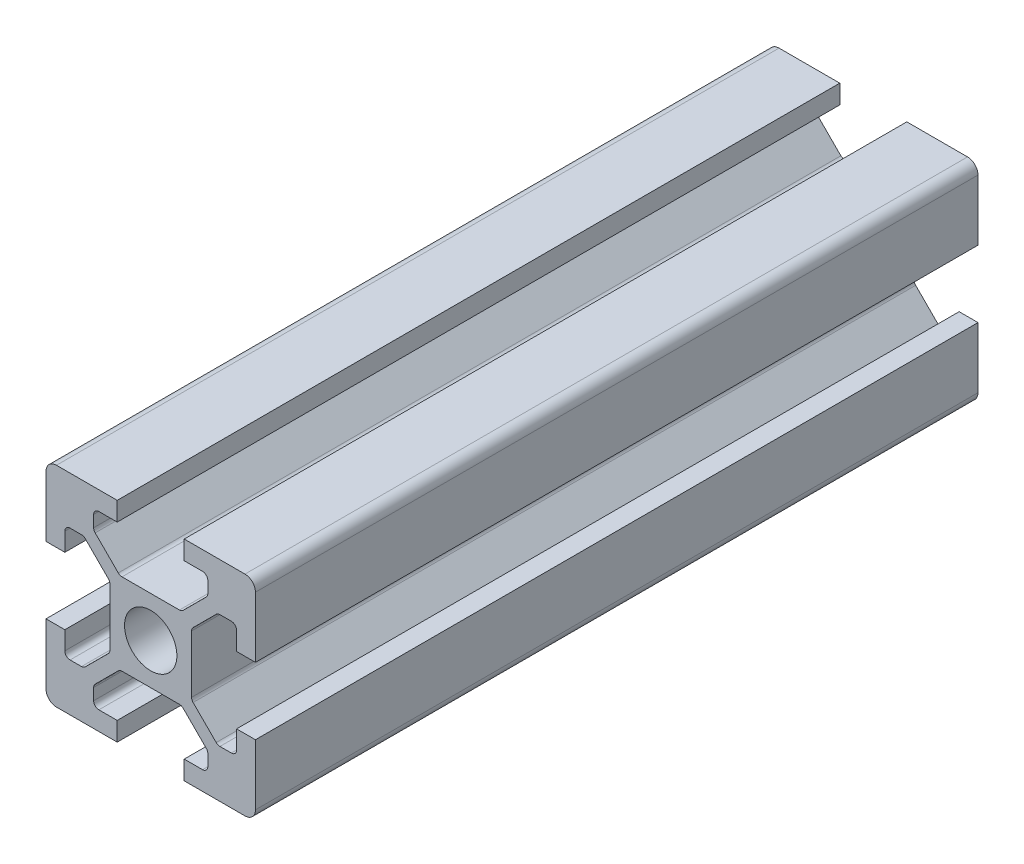
SolidWorks part; units mm, degrees
material "1060 Alloy"
ref_plane "Front Plane" through (0, 0, 0) normal (0, 0, 1) x (1, 0, 0)
ref_plane "Top Plane" through (0, 0, 0) normal (0, 1, 0) x (1, 0, 0)
ref_plane "Right Plane" through (0, 0, 0) normal (1, 0, 0) x (0, 0, -1)
sketch "Sketch1" plane through (0, 0, 0) normal (0, 0, 1) x (1, 0, 0)
  line L0 (20, 0) -> (-8.059, 28.059) construction
  line L1 (0, 0) -> (6.8, 0)
  line L2 (0, 0) -> (0, 6.8)
  line L3 (0, 20) -> (6.8, 20)
  line L4 (20, 0) -> (20, 6.8)
  line L5 (6.8, 20) -> (6.8, 18.2)
  line L6 (20, 20) -> (8.2322, 8.2322) construction
  line L7 (12.95, 6.1) -> (7.05, 6.1)
  line L8 (13.9, 7.05) -> (13.9, 12.95)
  line L9 (12.95, 13.9) -> (7.05, 13.9)
  line L10 (6.1, 7.05) -> (6.1, 12.95)
  line L11 (13.9, 6.1) -> (6.1, 13.9) construction
  line L12 (13.9, 13.9) -> (6.1, 6.1) construction
  line L13 (4.55, 16.4) -> (7.05, 13.9)
  line L14 (13.2, 18.2) -> (13.2, 20)
  line L15 (1.8, 6.8) -> (0, 6.8)
  line L16 (0, 13.2) -> (0, 20)
  line L17 (0, 13.2) -> (1.8, 13.2)
  line L18 (10, 10) -> (10, 13.9) construction
  line L19 (16.4, 4.55) -> (13.9, 7.05)
  line L20 (4.55, 16.4) -> (4.55, 18.2)
  line L21 (4.55, 18.2) -> (6.8, 18.2)
  line L22 (13.2, 18.2) -> (15.45, 18.2)
  line L23 (15.45, 18.2) -> (15.45, 16.4)
  line L24 (15.45, 16.4) -> (12.95, 13.9)
  line L25 (16.4, 4.55) -> (18.2, 4.55)
  line L26 (18.2, 4.55) -> (18.2, 6.8)
  line L27 (20, 6.8) -> (18.2, 6.8)
  line L28 (18.2, 13.2) -> (20, 13.2)
  line L29 (18.2, 13.2) -> (18.2, 15.45)
  line L30 (18.2, 15.45) -> (16.4, 15.45)
  line L31 (16.4, 15.45) -> (13.9, 12.95)
  line L32 (1.8, 4.55) -> (3.6, 4.55)
  line L33 (3.6, 15.45) -> (6.1, 12.95)
  line L34 (3.6, 15.45) -> (1.8, 15.45)
  line L35 (1.8, 15.45) -> (1.8, 13.2)
  line L36 (0, 13.2) -> (1.8, 13.2)
  line L37 (1.8, 6.8) -> (0, 6.8)
  line L38 (3.6, 4.55) -> (6.1, 7.05)
  line L39 (1.8, 6.8) -> (1.8, 4.55)
  line L40 (15.45, 3.6) -> (12.95, 6.1)
  line L41 (4.55, 3.6) -> (7.05, 6.1)
  line L42 (4.55, 1.8) -> (4.55, 3.6)
  line L43 (6.8, 1.8) -> (4.55, 1.8)
  line L44 (6.8, 1.8) -> (6.8, 0)
  line L45 (15.45, 3.6) -> (15.45, 1.8)
  line L46 (15.45, 1.8) -> (13.2, 1.8)
  line L47 (13.2, 0) -> (13.2, 1.8)
  line L48 (13.2, 20) -> (20, 20)
  line L49 (20, 13.2) -> (20, 20)
  line L50 (13.2, 0) -> (20, 0)
  line L51 (6.1, 6.1) -> (-5.5045, -5.5045) construction
  circle A0 centre (10, 10) radius 2.5
  point P25 (10, 16.4)
  point P39 (13.2, 19.1)
  point P46 (0.9, 6.8)
  dimension "D3" = 5
  dimension "D2" = 20
  dimension "D4" = 7.8
  dimension "D5" = 7.8
  dimension "D6" = 6.8
  dimension "D7" = 6.8
  dimension "D8" = 1.8
  dimension "D9" = 10.9
  dimension "D10" = 1.8
  dimension "D11" = 10.9
  dimension "D12" = 20
extrude "Boss-Extrude1" add sketch "Sketch1" along normal blind 69 contours L47 L50 L4 L27 L26 L25 L19 L8 L31 L30 L29 L28 L49 L48 L14 L22 L23 L24 L9 L13 L20 L21 L5 L3 L16 L17 L35 L34 L33 L10 L38 L32 L39 L15 L2 L1 L44 L43 L42 L41 L7 L40 L45 L46 A0
fillet "Fillet1" radius 1 4 edges at (20, 20, 34.5) (20, 0, 34.5) (0, 0, 34.5) (0, 20, 34.5)
fillet "Fillet2" radius 0.5 6 edges at (4.55, 18.2, 34.5) (4.55, 16.4, 34.5) (7.05, 13.9, 34.5) (15.45, 18.2, 34.5) (15.45, 16.4, 34.5) (12.95, 13.9, 34.5)
fillet "Fillet3" radius 0.5 6 edges at (18.2, 15.45, 34.5) (16.4, 15.45, 34.5) (13.9, 12.95, 34.5) (18.2, 4.55, 34.5) (13.9, 7.05, 34.5) (16.4, 4.55, 34.5)
fillet "Fillet4" radius 0.5 6 edges at (1.8, 15.45, 34.5) (3.6, 15.45, 34.5) (6.1, 12.95, 34.5) (3.6, 4.55, 34.5) (1.8, 4.55, 34.5) (6.1, 7.05, 34.5)
fillet "Fillet5" radius 0.5 6 edges at (7.05, 6.1, 34.5) (4.55, 3.6, 34.5) (4.55, 1.8, 34.5) (15.45, 1.8, 34.5) (15.45, 3.6, 34.5) (12.95, 6.1, 34.5)
